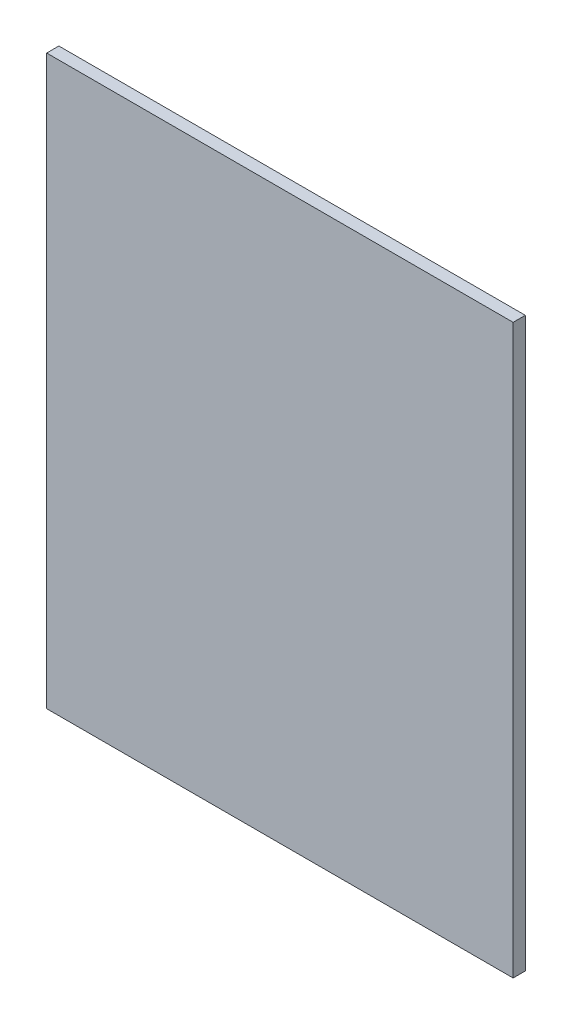
SolidWorks part; units mm, degrees
ref_plane "Front Plane" through (0, 0, 0) normal (0, 0, 1) x (1, 0, 0)
ref_plane "Top Plane" through (0, 0, 0) normal (0, 1, 0) x (1, 0, 0)
ref_plane "Right Plane" through (0, 0, 0) normal (1, 0, 0) x (0, 0, -1)
sketch "Sketch2" plane through (0, 0, 0) normal (0, 0, 1) x (1, 0, 0)
  line L0 (151.8841, -292.9262) -> (36.8841, -292.9262)
  line L1 (151.8841, -292.9262) -> (151.8841, -432.9262)
  line L2 (36.8841, -292.9262) -> (36.8841, -432.9262)
  line L3 (151.8841, -432.9262) -> (36.8841, -432.9262)
  dimension "D1" = 115
  dimension "D2" = 140
extrude "Boss-Extrude1" add sketch "Sketch2" along normal blind 3
